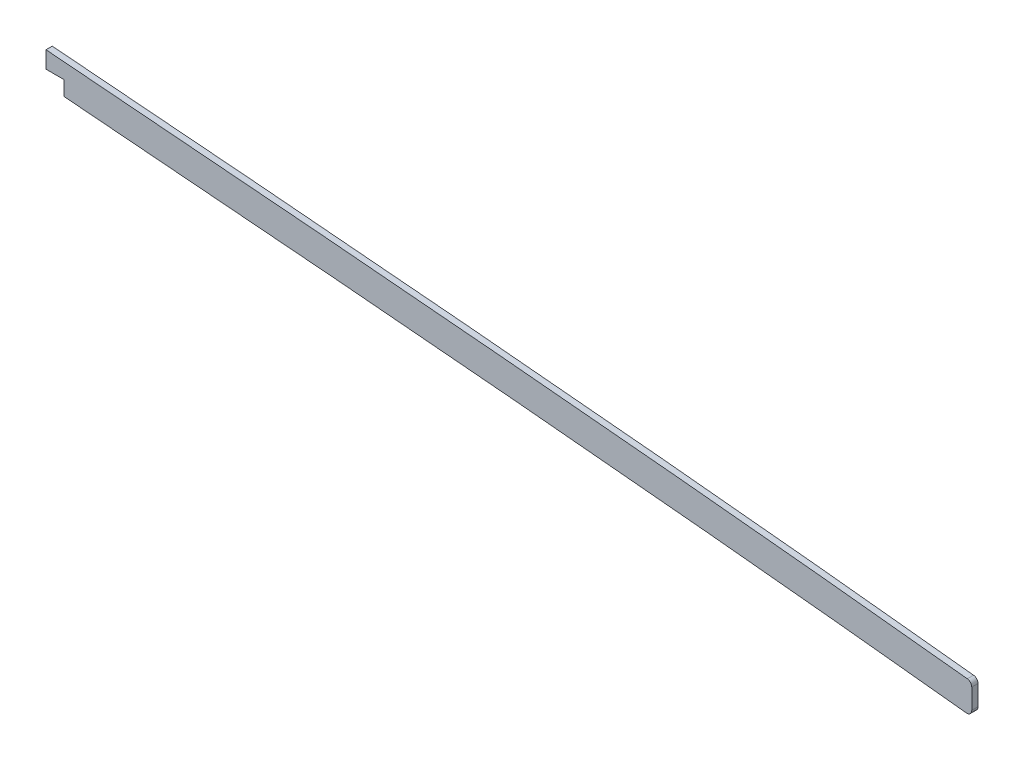
SolidWorks part; units mm, degrees
ref_plane "Front Plane" through (0, 0, 0) normal (0, 0, 1) x (1, 0, 0)
ref_plane "Top Plane" through (0, 0, 0) normal (0, 1, 0) x (1, 0, 0)
ref_plane "Right Plane" through (0, 0, 0) normal (1, 0, 0) x (0, 0, -1)
sketch "Sketch2" plane through (0, 0, 0) normal (0, 0, 1) x (1, 0, 0)
  line L0 (0, 0) -> (266.9553, 0) construction
  line L1 (825.5, 263.7287) -> (825.5, 174.6622)
  line L2 (2491.74, 117.5472) -> (2491.74, 52.664)
  spline S0 degree 5 poles (818.067, 264.7065) (827.0431, 263.4992) (836.0291, 262.3734) (845.0868, 261.3058) (891.3865, 256.087) (937.6862, 251.7792) (973.4521, 248.2277) (1071.9467, 239.0511) (1170.4413, 229.7315) (1231.7919, 224.5039) (1324.8993, 216.7906) (1418.0067, 209.0401) (1449.7429, 206.3618) (1636.9286, 190.5211) (1824.1143, 175.4092) (1979.9669, 164.2997) (2156.2686, 150.4144) (2332.5703, 133.8572) (2354.213, 131.7851) (2436.3555, 123.724) (2518.4981, 114.8591) (2579.4813, 107.7425) (2639.6368, 100.3834) (2699.7923, 92.6045) knots 77.930822 77.930822 77.930822 77.930822 77.930822 77.930822 82.465793 82.465793 82.465793 100.79329 100.79329 100.79329 131.098954 131.098954 131.098954 146.769198 146.769198 146.769198 223.533959 223.533959 223.533959 233.943117 233.943117 233.943117 264.216209 264.216209 264.216209 264.216209 264.216209 264.216209 weights 1 1 1 1 1 1 1 1 1 1 1 1 1 1 1 1 1 1 1 1 1 1 1 1
  spline S1 degree 1 poles (816.0355, 249.6025) (2697.8379, 77.4903) knots 0 0 1 1 construction
  spline S2 degree 3 poles (816.0355, 249.6025) (820.896, 248.9488) (830.6112, 247.6997) (845.2811, 245.9534) (860.0865, 244.2956) (879.8307, 242.1866) (904.37, 239.6983) (933.571, 236.8322) (962.6427, 234.0237) (991.7626, 231.242) (1021.072, 228.4759) (1060.3764, 224.797) (1109.513, 220.1844) (1168.5112, 214.8171) (1227.5001, 209.6621) (1306.1332, 203.0212) (1404.3615, 194.9207) (1522.2399, 184.9181) (1640.1829, 175.167) (1758.1654, 165.7576) (1876.1554, 156.5909) (1994.0875, 147.4533) (2092.2687, 139.6242) (2170.748, 133.0797) (2219.7717, 128.8422) (2258.984, 125.3472) (2288.3795, 122.6709) (2317.8122, 119.9317) (2347.5515, 117.1004) (2377.1599, 114.2101) (2406.4697, 111.269) (2435.8183, 108.2401) (2474.9139, 104.0902) (2523.7162, 98.6933) (2582.0419, 91.9123) (2640.0752, 84.8576) (2678.5742, 79.9814) (2697.8379, 77.4903) knots 77.930822 77.930822 77.930822 77.930822 79.386176 80.841531 82.296885 83.75224 86.662949 89.573658 92.484367 95.395077 98.305786 101.216495 107.037913 112.859332 118.68075 124.502168 136.145005 147.787842 159.430678 171.073515 182.716352 194.359189 206.002025 211.823444 217.644862 220.555571 223.46628 226.37699 229.287699 232.198408 235.109117 238.019826 240.930535 246.751954 252.573372 258.39479 264.216209 264.216209 264.216209 264.216209
  spline S3 degree 5 poles (818.067, -264.7065) (827.0431, -263.4992) (836.0291, -262.3734) (845.0868, -261.3058) (891.3865, -256.087) (937.6862, -251.7792) (973.4521, -248.2277) (1071.9467, -239.0511) (1170.4413, -229.7315) (1231.7919, -224.5039) (1324.8993, -216.7906) (1418.0067, -209.0401) (1449.7429, -206.3618) (1636.9286, -190.5211) (1824.1143, -175.4092) (1979.9669, -164.2997) (2156.2686, -150.4144) (2332.5703, -133.8572) (2354.213, -131.7851) (2436.3555, -123.724) (2518.4981, -114.8591) (2579.4813, -107.7425) (2639.6368, -100.3834) (2699.7923, -92.6045) knots 77.930822 77.930822 77.930822 77.930822 77.930822 77.930822 82.465793 82.465793 82.465793 100.79329 100.79329 100.79329 131.098954 131.098954 131.098954 146.769198 146.769198 146.769198 223.533959 223.533959 223.533959 233.943117 233.943117 233.943117 264.216209 264.216209 264.216209 264.216209 264.216209 264.216209 weights 1 1 1 1 1 1 1 1 1 1 1 1 1 1 1 1 1 1 1 1 1 1 1 1
  point P2 (0, 0)
  dimension "D1" = 818.067
  dimension "D2" = 825.5
  dimension "D3" = 2491.74
  dimension "D4" = 15.24
extrude "Boss-Extrude1" add sketch "Sketch2" along normal mid plane 3.175 contours L1 S2 L2 S0
fillet "Fillet1" radius 2.54 4 edges at (2491.74, 102.2148, 0) (825.5, 248.3644, 0)
sketch "Sketch3" plane through (0, 0, 1.5875) normal (0, 0, 1) x (1, 0, 0)
  line L0 (2021.3026, 160.5495) -> (2021.3026, 169.9004)
  line L7 (2021.3026, 160.5495) -> (2021.3026, 151.9732)
  line L8 (2021.3026, 151.9732) -> (2030.429, 151.9732)
  line L9 (2030.429, 151.9732) -> (2030.429, 144.5379)
  line L10 (2021.3026, 169.9004) -> (799.6266, 282.3894)
  line L11 (799.6266, 282.3894) -> (799.6266, 218.4497)
  line L12 (799.6266, 218.4497) -> (2030.429, 140.1936)
  line L13 (2030.429, 140.1936) -> (2030.429, 144.5379)
  spline S0 degree 5 poles (828.3591, 263.3639) (835.3006, 262.485) (842.2713, 261.6451) (849.2939, 260.8336) (893.49, 255.8914) (937.6862, 251.7793) (973.4521, 248.2278) (1071.9467, 239.0512) (1170.4413, 229.7316) (1231.792, 224.504) (1324.8993, 216.7907) (1418.0067, 209.0402) (1449.7429, 206.3619) (1636.9286, 190.5212) (1824.1143, 175.4092) (1979.967, 164.2997) (2156.2686, 150.4145) (2332.5703, 133.8572) (2354.213, 131.7851) (2393.888, 127.8915) (2433.5631, 123.8105) (2452.2167, 121.8477) (2470.8575, 119.8423) (2489.4775, 117.7961) knots 78.969534 78.969534 78.969534 78.969534 78.969534 78.969534 82.465793 82.465793 82.465793 100.79329 100.79329 100.79329 131.098954 131.098954 131.098954 146.769198 146.769198 146.769198 223.533959 223.533959 223.533959 233.943117 233.943117 233.943117 243.183575 243.183575 243.183575 243.183575 243.183575 243.183575 weights 1 1 1 1 1 1 1 1 1 1 1 1 1 1 1 1 1 1 1 1 1 1 1 1 construction
  spline S1 degree 3 poles (827.7231, 248.0832) (828.6907, 247.9616) (834.5293, 247.2333) (845.2811, 245.9534) (860.0865, 244.2956) (879.8307, 242.1866) (904.37, 239.6983) (933.571, 236.8322) (962.6427, 234.0237) (991.7626, 231.242) (1021.072, 228.4759) (1060.3764, 224.797) (1109.513, 220.1844) (1168.5112, 214.8171) (1227.5001, 209.6621) (1306.1332, 203.0212) (1404.3615, 194.9207) (1522.2399, 184.9181) (1640.1829, 175.167) (1758.1654, 165.7576) (1876.1554, 156.5909) (1994.0875, 147.4533) (2092.2687, 139.6242) (2170.748, 133.0797) (2219.7717, 128.8422) (2258.984, 125.3472) (2288.3795, 122.6709) (2317.8122, 119.9317) (2347.5515, 117.1004) (2377.1599, 114.2101) (2406.4697, 111.269) (2435.8183, 108.2401) (2463.3021, 105.3227) (2480.9973, 103.397) (2488.9223, 102.5252) knots 79.096923 79.096923 79.096923 79.096923 79.386176 80.841531 82.296885 83.75224 86.662949 89.573658 92.484367 95.395077 98.305786 101.216495 107.037913 112.859332 118.68075 124.502168 136.145005 147.787842 159.430678 171.073515 182.716352 194.359189 206.002025 211.823444 217.644862 220.555571 223.46628 226.37699 229.287699 232.198408 235.109117 238.019826 240.930535 243.293903 243.293903 243.293903 243.293903 construction
extrude "Cut-Extrude1" cut sketch "Sketch3" against normal blind 7.62 contours L12 L13 L9 L8 L7 L0 L10 L11
